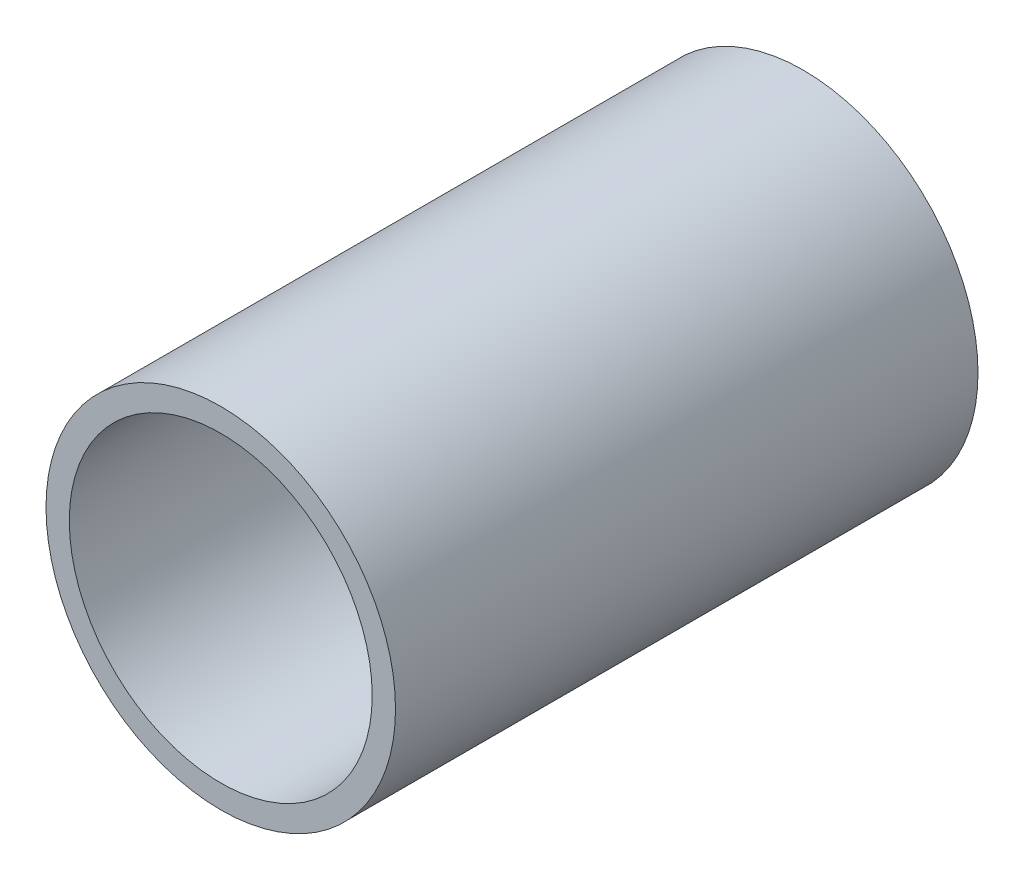
SolidWorks part; units mm, degrees
ref_plane "Plan de face" through (0, 0, 0) normal (0, 0, 1) x (1, 0, 0)
ref_plane "Plan de dessus" through (0, 0, 0) normal (0, 1, 0) x (1, 0, 0)
ref_plane "Plan de droite" through (0, 0, 0) normal (1, 0, 0) x (0, 0, -1)
sketch "Esquisse1" plane through (0, 0, 0) normal (0, 0, 1) x (1, 0, 0)
  circle A0 centre (0, 0) radius 13
  circle A1 centre (0, 0) radius 15
  dimension "D1" = 26
  dimension "D2" = 30
extrude "Boss.-Extru.1" add sketch "Esquisse1" along normal blind 50
